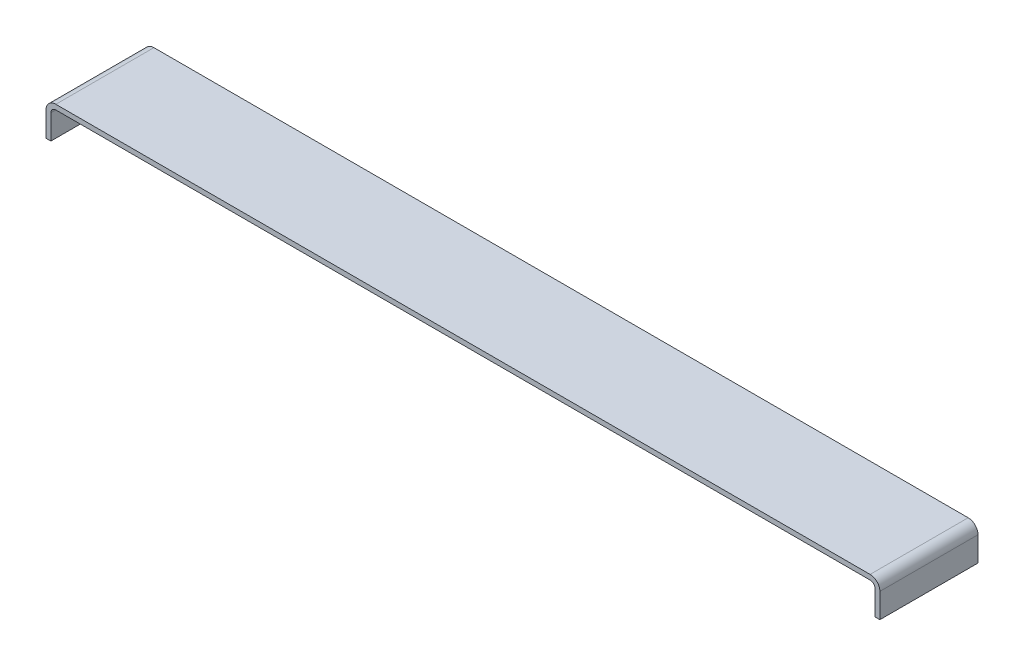
SolidWorks part; units mm, degrees
ref_plane "Plano frontal" through (0, 0, 0) normal (0, 0, 1) x (1, 0, 0)
ref_plane "Plano superior" through (0, 0, 0) normal (0, 1, 0) x (1, 0, 0)
ref_plane "Plano direito" through (0, 0, 0) normal (1, 0, 0) x (0, 0, -1)
sketch "Esboço1" plane through (0, 0, 0) normal (0, 0, 1) x (1, 0, 0)
  line L0 (0, 0) -> (0, 5)
  line L1 (2, 7) -> (168, 7)
  line L2 (170, 5) -> (170, 0)
  line L3 (1, 0) -> (1, 5)
  line L4 (2, 6) -> (168, 6)
  line L5 (169, 5) -> (169, 0)
  line L6 (0, 0) -> (1, 0)
  line L7 (169, 0) -> (170, 0)
  arc A0 (2, 7) -> (0, 5) centre (2, 5) ccw
  arc A1 (170, 5) -> (168, 7) centre (168, 5) ccw
  arc A2 (2, 6) -> (1, 5) centre (2, 5) ccw
  arc A3 (169, 5) -> (168, 6) centre (168, 5) ccw
  point P7 (0, 7)
  point P10 (170, 7)
  dimension "D4" = 2
  dimension "D5" = 2
  dimension "D1" = 170
  dimension "D2" = 7
  dimension "D3" = 7
extrude "Ressalto-extrusão1" add sketch "Esboço1" along normal blind 20
